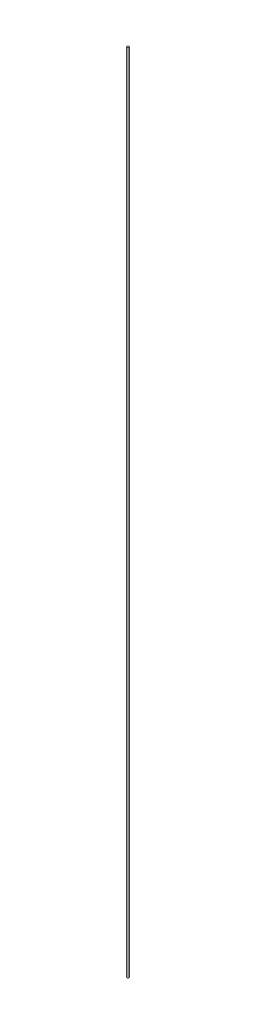
SolidWorks part; units mm, degrees
material "Hexcel AS4C (3000 Filaments)"
ref_plane "Front Plane" through (0, 0, 0) normal (0, 0, 1) x (1, 0, 0)
ref_plane "Top Plane" through (0, 0, 0) normal (0, 1, 0) x (1, 0, 0)
ref_plane "Right Plane" through (0, 0, 0) normal (1, 0, 0) x (0, 0, -1)
sketch "Sketch2" plane through (0, 0, 0) normal (0, 1, 0) x (1, 0, 0)
  circle A0 centre (0, 0) radius 1.27
  dimension "D1" = 2.54
extrude "Boss-Extrude3" add sketch "Sketch2" along normal blind 1136.65
